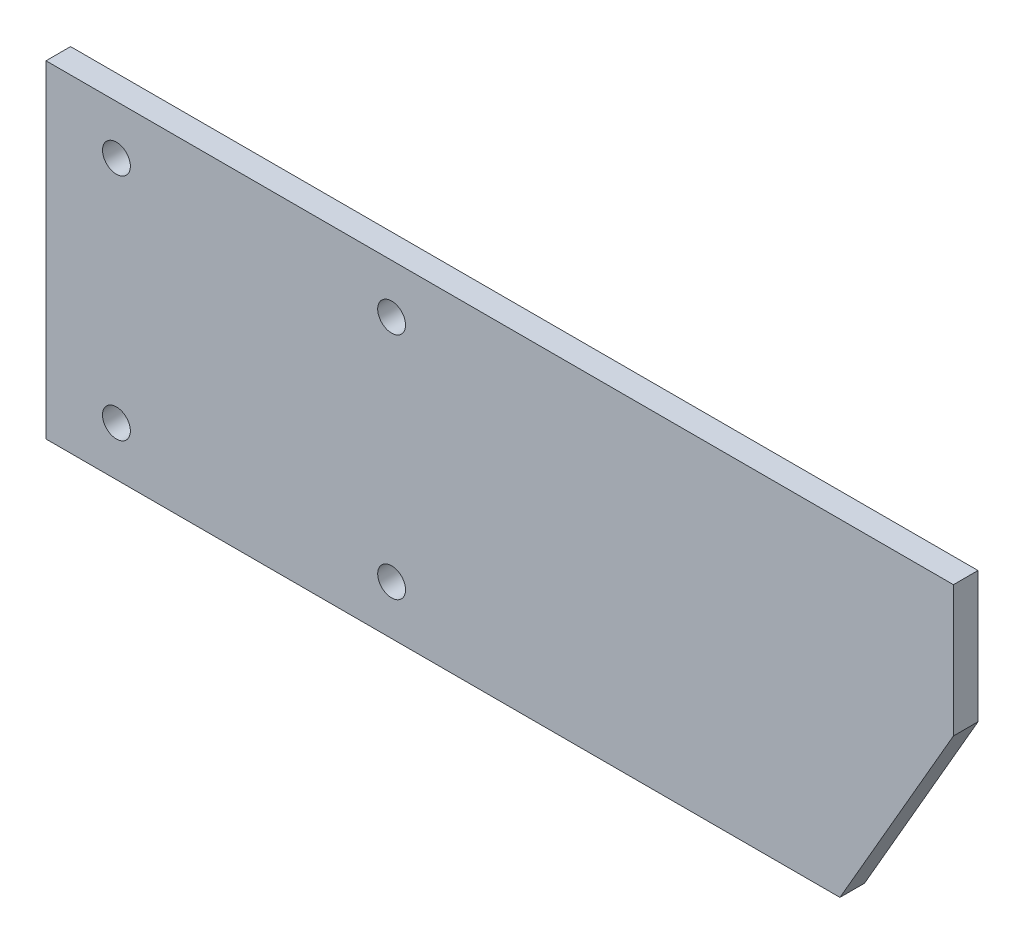
SolidWorks part; units mm, degrees
ref_plane "Front Plane" through (0, 0, 0) normal (0, 0, 1) x (1, 0, 0)
ref_plane "Top Plane" through (0, 0, 0) normal (0, 1, 0) x (1, 0, 0)
ref_plane "Right Plane" through (0, 0, 0) normal (1, 0, 0) x (0, 0, -1)
sketch "Sketch1" plane through (0, 0, 0) normal (0, 0, 1) x (1, 0, 0)
  line L0 (-127, 100) -> (427, 100)
  line L1 (-127, 100) -> (-127, -100)
  line L2 (-127, -100) -> (357.718, -100)
  line L3 (357.718, -100) -> (427, 20)
  line L4 (427, 20) -> (427, 100)
  circle A0 centre (-84, 70) radius 8.5
  circle A1 centre (84, 70) radius 8.5
  circle A2 centre (84, -70) radius 8.5
  circle A3 centre (-84, -70) radius 8.5
  dimension "D7" = 17
  dimension "D1" = 554
  dimension "D2" = 200
  dimension "D3" = 127
  dimension "D4" = 100
  dimension "D5" = 60
  dimension "D6" = 80
  dimension "D8" = 70
  dimension "D9" = 70
  dimension "D10" = 84
  dimension "D11" = 84
extrude "Extrude1" add sketch "Sketch1" along normal blind 15
